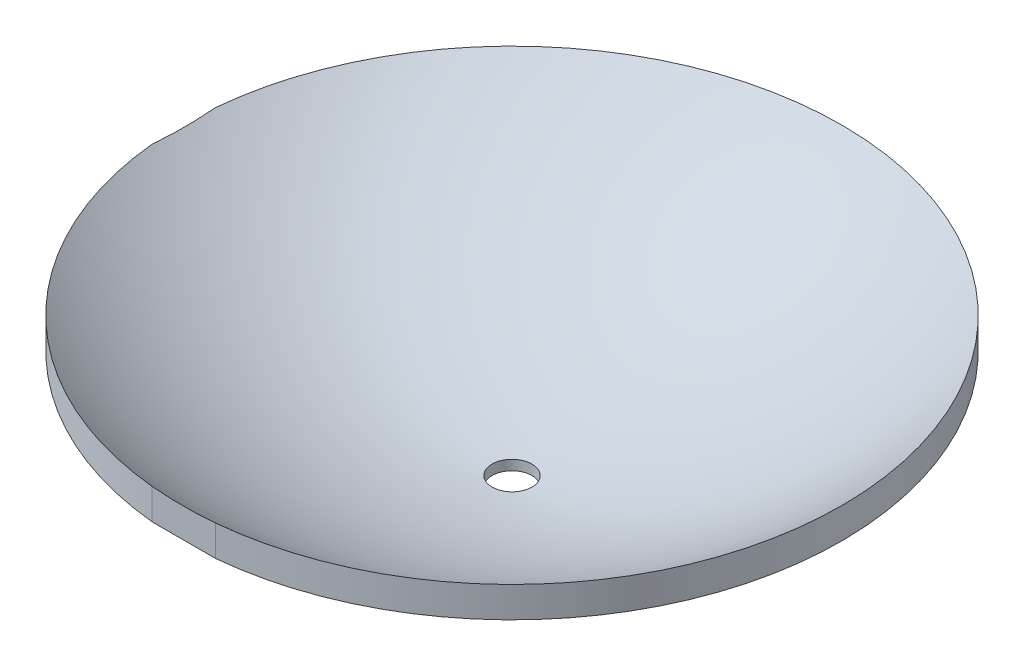
SolidWorks part; units mm, degrees
material "ABS"
ref_plane "Vue de dessus" through (0, 0, 0) normal (0, 0, 1) x (1, 0, 0)
ref_plane "Vue de face" through (0, 0, 0) normal (0, 1, 0) x (1, 0, 0)
ref_plane "Plan de droite" through (0, 0, 0) normal (1, 0, 0) x (0, 0, -1)
sketch "Esquisse2" plane through (0, 0, 0) normal (0, 0, 1) x (1, 0, 0)
  line L0 (0, 0) -> (0, -97) construction
  line L1 (-15.75, -97) -> (-13, -97)
  line L2 (-215, 0) -> (-215, -20)
  line L3 (-15.75, -93) -> (-15.75, -97)
  line L4 (-13, -90.522) -> (-13, -97)
  line L5 (-212.5, -20) -> (-212.1, -6.3617)
  line L6 (-215, -20) -> (-212.5, -20)
  arc A0 (-215, 0) -> (-13, -90.522) centre (17.8207, 248.897) ccw
  arc A1 (-212.1, -6.3617) -> (-15.75, -93) centre (17.8207, 248.897) ccw
  circle A3 centre (17.8207, 248.897) radius 343.5412 construction
  circle A4 centre (17.8207, 248.897) radius 340.8155 construction
  point P4 (362.8246, 248.4294)
  point P16 (350.8135, 348.8711)
  dimension "D1" = 97
  dimension "D2" = 215
  dimension "D3" = 20
  dimension "D4" = 15.75
  dimension "D5" = 13
  dimension "D6" = 4
  dimension "D7" = 2.5
  dimension "D8" = 2.9
revolve "Révolution1" add sketch "Esquisse2" angle 360 about L0
sketch "Esquisse3" plane through (0, 0, 0) normal (0, 1, 0) x (1, 0, 0)
  line L1 (-69.719, -250.9288) -> (105.3743, -250.9288)
  line L2 (-69.719, -250.9288) -> (-69.719, -214)
  line L3 (-69.719, -214) -> (105.3743, -214)
  line L4 (105.3743, -250.9288) -> (105.3743, -214)
  dimension "D1" = 214
extrude "Enlèv. mat.-Extru.1" cut sketch "Esquisse3" against normal blind 34
ref_plane "Plan1" through (-179.7378, -96.3882, 3.4602) normal (-0.8811, -0.4725, 0.017) x (0.017, -0.0675, -0.9976)
ref_plane "Plan2" through (-179.7378, -96.3882, 3.4602) normal (-0.8811, -0.4725, 0.017) x (0.017, -0.0675, -0.9976)
sketch "Esquisse4" plane through (0, 0, 0) normal (0, 1, 0) x (1, 0, 0)
  line L1 (-261.3077, 121.3611) -> (-214, 121.3611)
  line L2 (-261.3077, 121.3611) -> (-261.3077, -158.1844)
  line L3 (-261.3077, -158.1844) -> (-214, -158.1844)
  line L4 (-214, 121.3611) -> (-214, -158.1844)
  dimension "D1" = 214
extrude "Enlèv. mat.-Extru.2" cut sketch "Esquisse4" against normal blind 41
